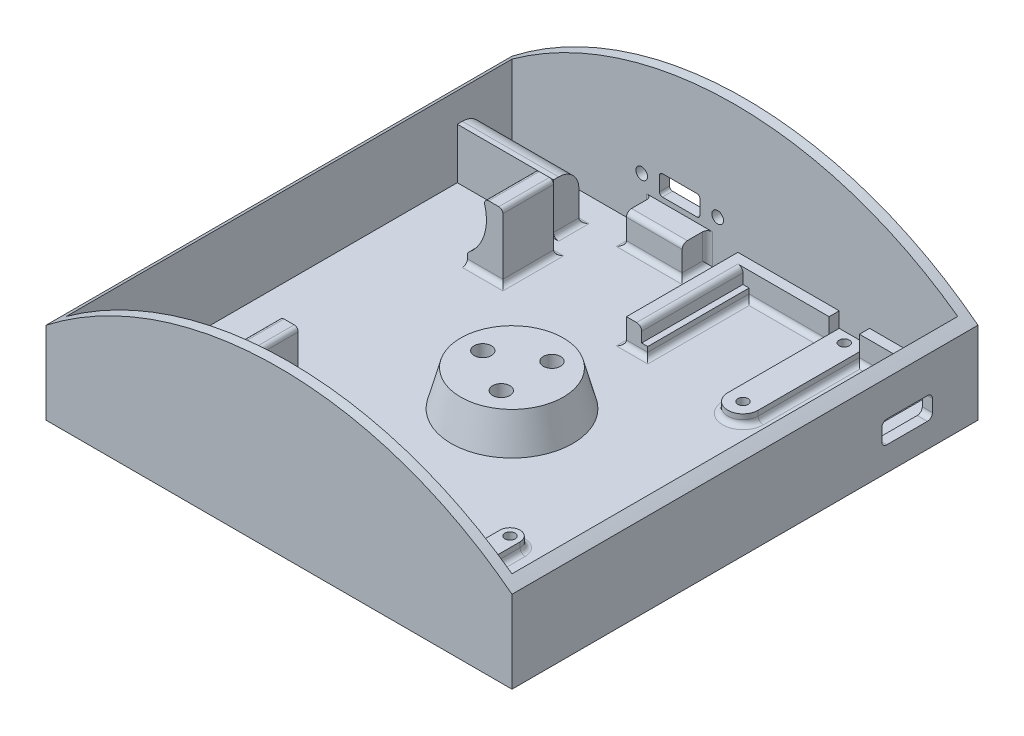
SolidWorks part; units mm, degrees
ref_plane "Front Plane" through (0, 0, 0) normal (0, 0, 1) x (1, 0, 0)
ref_plane "Top Plane" through (0, 0, 0) normal (0, 1, 0) x (1, 0, 0)
ref_plane "Right Plane" through (0, 0, 0) normal (1, 0, 0) x (0, 0, -1)
sketch "Sketch1" plane through (0, 0, 0) normal (0, 1, 0) x (1, 0, 0)
  line L1 (-46, 46) -> (46, 46)
  line L2 (-46, 46) -> (-46, -46)
  line L3 (-46, -46) -> (46, -46)
  line L4 (46, 46) -> (46, -46)
  line L5 (-46, 46) -> (46, -46) construction
  line L6 (-46, -46) -> (46, 46) construction
  point P0 (0, 0)
  dimension "D1" = 92
  dimension "D2" = 92
extrude "Boss-Extrude1" add sketch "Sketch1" along normal blind 2
sketch "Sketch7" plane through (0, 2, 0) normal (0, 1, 0) x (1, 0, 0)
  circle A0 centre (0, 0) radius 12
  dimension "D1" = 24
extrude "Boss-Extrude2" add sketch "Sketch7" along normal blind 7 draft 15
sketch "Sketch4" plane through (0, 2, 0) normal (0, 1, 0) x (1, 0, 0)
  circle A0 centre (-5.77, 0) radius 1.7
  circle A1 centre (2.885, 4.997) radius 1.7
  circle A2 centre (2.885, -4.997) radius 1.7
  point P10 (0, 0)
  dimension "D2" = 3.4
  dimension "D1" = 5.77
extrude "Cut-Extrude3" cut sketch "Sketch4" against normal through all both and the other way through all
sketch "Sketch6" plane through (0, 2, 0) normal (0, 1, 0) x (1, 0, 0)
  circle A0 centre (2.885, 4.997) radius 3.5
  circle A1 centre (-5.77, 0) radius 3.5
  circle A2 centre (2.885, -4.997) radius 3.5
  dimension "D1" = 7
  dimension "D2" = 7
  dimension "D3" = 7
extrude "Cut-Extrude4" cut sketch "Sketch6" against normal through all from offset 0.4 offset against normal yes
sketch "Sketch8" plane through (0, 2, 0) normal (0, 1, 0) x (1, 0, 0)
  line L0 (-46, 0) -> (46, 0) construction
  line L1 (-46, 46) -> (-46, -46) construction
  line L2 (46, -46) -> (46, 46) construction
  line L3 (-44, -33.2) -> (-25, -33.2)
  line L4 (-44, 38.2) -> (-25, 38.2)
  line L5 (-44, 38.2) -> (-44, 33.2)
  line L6 (-44, 33.2) -> (-25, 33.2)
  line L7 (-25, 38.2) -> (-25, 33.2)
  line L8 (-44, 38.2) -> (-25, 33.2) construction
  line L9 (-44, 33.2) -> (-25, 38.2) construction
  line L10 (-25, -38.2) -> (-25, -33.2)
  line L11 (-44, -38.2) -> (-44, -33.2)
  line L12 (-44, -38.2) -> (-25, -38.2)
  circle A0 centre (0, 0) radius 25 construction
  point P9 (-34.5, 35.7)
  dimension "D1" = 50
  dimension "D2" = 19
  dimension "D3" = 25
  dimension "D4" = 5
  dimension "D5" = 33.2
extrude "Boss-Extrude3" add sketch "Sketch8" along normal blind 10
fillet "Fillet1" radius 4 2 edges at (-34.5, 12, -38.2) (-34.5, 12, 38.2)
sketch "Sketch12" plane through (0, 2, 0) normal (0, 1, 0) x (1, 0, 0)
  line L0 (-46, 0) -> (46, 0) construction
  line L5 (-46, 46) -> (-46, -46) construction
  line L6 (46, -46) -> (46, 46) construction
  line L12 (-25, 33.2) -> (-25, 38.2) construction
  line L13 (-29, 30.2) -> (-22, 30.2)
  line L14 (-29, 30.2) -> (-29, 20.2)
  line L15 (-29, 20.2) -> (-22, 20.2)
  line L16 (-22, 30.2) -> (-22, 20.2)
  line L17 (-44, 33.2) -> (-25, 33.2) construction
  line L18 (-29, -20.2) -> (-22, -20.2)
  line L19 (-22, -30.2) -> (-22, -20.2)
  line L20 (-29, -30.2) -> (-29, -20.2)
  line L21 (-29, -30.2) -> (-22, -30.2)
  dimension "D1" = 10
  dimension "D2" = 7
  dimension "D3" = 4
  dimension "D4" = 3
extrude "Boss-Extrude6" add sketch "Sketch12" along normal blind 13
sketch "Sketch16" plane through (0, 0, 30.2) normal (0, 0, 1) x (1, 0, 0)
  line L0 (-46, 2) -> (46, 2) construction
  line L1 (-25, 8) -> (-25, 2) construction
  circle A0 centre (-34.5, 11.5) radius 9.25
  dimension "D1" = 18.5
  dimension "D2" = 9.5
  dimension "D3" = 9.5
extrude "Cut-Extrude5" cut sketch "Sketch16" against normal up to surface (60.4 mm away) up to face at (-25.5, 8.5, -30.2)
fillet "Fillet3" radius 0.8 6 edges at (-25.9377, 15, -25.2) (-22, 15, -25.2) (-22, 15, 25.2) (-25.9377, 15, 25.2) (-29, 4.0628, 25.2) (-29, 4.0628, -25.2)
sketch "Sketch17" plane through (0, 2, 0) normal (0, 1, 0) x (1, 0, 0)
  line L0 (-44, 44) -> (44, 44)
  line L1 (-46, 46) -> (46, 46)
  line L2 (-46, 46) -> (-46, -46)
  line L3 (-46, -46) -> (46, -46)
  line L4 (46, 46) -> (46, -46)
  line L5 (44, 44) -> (44, -44)
  line L6 (-44, -44) -> (44, -44)
  line L7 (-44, 44) -> (-44, -44)
  dimension "D1" = 2
extrude "Boss-Extrude11" add sketch "Sketch17" along normal blind 30
sketch "Sketch19" plane through (0, 0, 46) normal (0, 0, 1) x (1, 0, 0)
  line L0 (-46, 0) -> (46, 0) construction
  circle A1 centre (0, -43) radius 75
  circle A2 centre (0, -43) radius 105
  dimension "D1" = 43
  dimension "D2" = 150
  dimension "D3" = 30
extrude "Cut-Extrude6" cut sketch "Sketch19" against normal up to surface (92 mm away) up to face at (0, 16, -46)
sketch "Sketch20" plane through (0, 2, 0) normal (0, 1, 0) x (1, 0, 0)
  line L0 (0.6, 44) -> (0.6, 22)
  line L1 (44, 44) -> (26.6, 44)
  line L2 (44, 44) -> (44, 42)
  line L3 (44, 42) -> (26.6, 42)
  line L7 (0.6, 22) -> (3.6, 22)
  line L8 (3.6, 42) -> (3.6, 22)
  line L9 (26.6, 44) -> (26.6, 42)
  line L10 (20.6, 44) -> (20.6, 42)
  line L11 (20.6, 44) -> (0.6, 44)
  line L12 (20.6, 42) -> (3.6, 42)
  dimension "D1" = 2
  dimension "D2" = 17.4
  dimension "D3" = 3
  dimension "D4" = 20
  dimension "D5" = 17
  dimension "D6" = 6
extrude "Boss-Extrude12" add sketch "Sketch20" along normal blind 5
sketch "Sketch21" plane through (0, 2, 0) normal (0, 1, 0) x (1, 0, 0)
  line L0 (3.6, 42) -> (20.6, 42) construction
  line L1 (26.6, 44) -> (20.6, 44)
  line L2 (26.6, 44) -> (26.6, 22)
  line L4 (20.6, 44) -> (20.6, 22)
  line L5 (44, 42) -> (41, 42)
  line L6 (44, 42) -> (44, 22)
  line L7 (44, 22) -> (41, 22)
  line L8 (41, 42) -> (41, 22)
  line L9 (3.6, 42) -> (4.8, 42)
  line L10 (3.6, 42) -> (3.6, 22)
  line L11 (3.6, 22) -> (4.8, 22)
  line L12 (4.8, 42) -> (4.8, 22)
  arc A0 (20.6, 22) -> (26.6, 22) centre (23.6, 22) ccw
  dimension "D7" = 3
  dimension "D1" = 1.2
  dimension "D2" = 20
  dimension "D4" = 20
  dimension "D5" = 3
  dimension "D6" = 20
  dimension "D8" = 6
extrude "Boss-Extrude13" add sketch "Sketch21" along normal blind 2
sketch "Sketch22" plane through (0, 4, 0) normal (0, 1, 0) x (1, 0, 0)
  line L0 (20.6, 42) -> (20.6, 22) construction
  circle A0 centre (23.6, 22) radius 1
  circle A1 centre (23.6, 42) radius 1
  dimension "D1" = 2
  dimension "D2" = 2
  dimension "D3" = 3
extrude "Cut-Extrude7" cut sketch "Sketch22" against normal through all
sketch "Sketch23" plane through (44, 0, 0) normal (-1, 0, 0) x (0, 0, 1)
  line L0 (-22, 4) -> (-42, 4) construction
  line L1 (-36, 9.2) -> (-28, 9.2)
  line L2 (-37, 8.2) -> (-37, 5.8)
  line L3 (-36, 4.8) -> (-28, 4.8)
  line L4 (-27, 8.2) -> (-27, 5.8)
  line L5 (-42, 7) -> (-42, 4) construction
  arc A0 (-36, 4.8) -> (-37, 5.8) centre (-36, 5.8) cw
  arc A1 (-28, 4.8) -> (-27, 5.8) centre (-28, 5.8) ccw
  arc A2 (-28, 9.2) -> (-27, 8.2) centre (-28, 8.2) cw
  arc A3 (-36, 9.2) -> (-37, 8.2) centre (-36, 8.2) ccw
  point P12 (-27, 4.8)
  point P15 (-27, 9.2)
  point P18 (-37, 9.2)
  dimension "D5" = 1
  dimension "D1" = 0.8
  dimension "D2" = 4.4
  dimension "D3" = 10
  dimension "D4" = 5
extrude "Cut-Extrude8" cut sketch "Sketch23" against normal through all
sketch "Sketch24" plane through (0, 2, 0) normal (0, 1, 0) x (1, 0, 0)
  line L0 (-44, -44) -> (44, -44) construction
  line L1 (21.6, -44) -> (25.6, -44)
  line L2 (21.6, -44) -> (21.6, -24)
  line L4 (25.6, -44) -> (25.6, -24)
  line L5 (44, -44) -> (44, 22) construction
  line L6 (1.6, -44) -> (5.6, -44)
  line L7 (1.6, -44) -> (1.6, -24)
  line L9 (5.6, -44) -> (5.6, -24)
  line L11 (44, 6.5) -> (37, 6.5)
  line L12 (44, 6.5) -> (44, -0.5)
  line L13 (44, -0.5) -> (37, -0.5)
  arc A0 (5.6, -24) -> (1.6, -24) centre (3.6, -24) ccw
  arc A1 (25.6, -24) -> (21.6, -24) centre (23.6, -24) ccw
  arc A2 (37, 6.5) -> (37, -0.5) centre (37, 3) ccw
  circle A4 centre (23.6, 22) radius 1 construction
  dimension "D1" = 20
  dimension "D2" = 20
  dimension "D3" = 4
  dimension "D4" = 4
  dimension "D5" = 18.4
  dimension "D6" = 16
  dimension "D7" = 7
  dimension "D8" = 7
  dimension "D9" = 15.5
extrude "Boss-Extrude14" add sketch "Sketch24" along normal blind 2
sketch "Sketch25" plane through (0, 4, 0) normal (0, 1, 0) x (1, 0, 0)
  circle A0 centre (3.6, -24) radius 1
  circle A1 centre (23.6, -24) radius 1
  circle A2 centre (37, 3) radius 1
  dimension "D1" = 2
  dimension "D2" = 2
  dimension "D3" = 2
extrude "Cut-Extrude9" cut sketch "Sketch25" against normal through all
sketch "Sketch27" plane through (0, 2, 0) normal (0, 1, 0) x (1, 0, 0)
  line L0 (0.6, 44) -> (-44, 44) construction
  line L1 (-16.4, 44) -> (-5.4, 44)
  line L2 (-16.4, 44) -> (-16.4, 39)
  line L3 (-16.4, 39) -> (-5.4, 39)
  line L4 (-5.4, 44) -> (-5.4, 39)
  line L5 (0.6, 44) -> (0.6, 22) construction
  dimension "D1" = 5
  dimension "D2" = 11
  dimension "D3" = 6
extrude "Boss-Extrude15" add sketch "Sketch27" along normal blind 6
sketch "Sketch28" plane through (0, 0, -44) normal (0, 0, 1) x (1, 0, 0)
  line L0 (-5.4, 8) -> (-16.4, 8) construction
  line L1 (-14.3, 13) -> (-7.5, 13)
  line L2 (-14.9, 12.4) -> (-14.9, 9.6)
  line L3 (-14.3, 9) -> (-7.5, 9)
  line L4 (-6.9, 12.4) -> (-6.9, 9.6)
  circle A0 centre (-18.4, 11) radius 1.15
  circle A1 centre (-3.4, 11) radius 1.15
  arc A2 (-6.9, 12.4) -> (-7.5, 13) centre (-7.5, 12.4) ccw
  arc A3 (-7.5, 9) -> (-6.9, 9.6) centre (-7.5, 9.6) ccw
  arc A4 (-14.3, 9) -> (-14.9, 9.6) centre (-14.3, 9.6) cw
  arc A5 (-14.9, 12.4) -> (-14.3, 13) centre (-14.3, 12.4) cw
  point P13 (-6.9, 13)
  point P18 (-14.9, 9)
  point P21 (-14.9, 13)
  dimension "D9" = 2.3
  dimension "D10" = 2.3
  dimension "D11" = 0.6
  dimension "D1" = 8
  dimension "D2" = 1.5
  dimension "D3" = 4
  dimension "D4" = 1
  dimension "D5" = 2
  dimension "D6" = 2
  dimension "D7" = 3.5
  dimension "D8" = 3.5
extrude "Cut-Extrude10" cut sketch "Sketch28" against normal through all
fillet "Fillet4" radius 1 1 edges at (3.6, 7, -32)
fillet "Fillet5" radius 1 6 edges at (-16.4, 5, -44) (-5.4, 5, -44) (-5.4, 2, -41.5) (-16.4, 2, -41.5) (-10.9, 2, -39) (-10.9, 8, -39)
fillet "Fillet6" radius 1 29 edges at (26.6, 2, -32) (23.6, 2, -19) (12.7, 2, -42) (33.8, 2, -42) (42.5, 2, -22) (41, 2, -32) (20.6, 2, -32) (4.8, 2, -32) (2.7, 2, -22) (0.6, 2, -33) (40.5, 2, -6.5) (33.5, 2, -3) (21.6, 2, 34) (23.6, 2, 22) (1.6, 2, 34) (3.6, 2, 22) (40.5, 2, 0.5) (25.6, 2, 34) (5.6, 2, 34) (-34.5, 2, 38.2) (-25, 2, 35.7) (-25.5, 2, 30.2) (-25.5, 2, 20.2) (-22, 2, 25.2) (-34.5, 2, -38.2) (-25, 2, -35.7) (-25.5, 2, -30.2) (-25.5, 2, -20.2) (-22, 2, -25.2)
